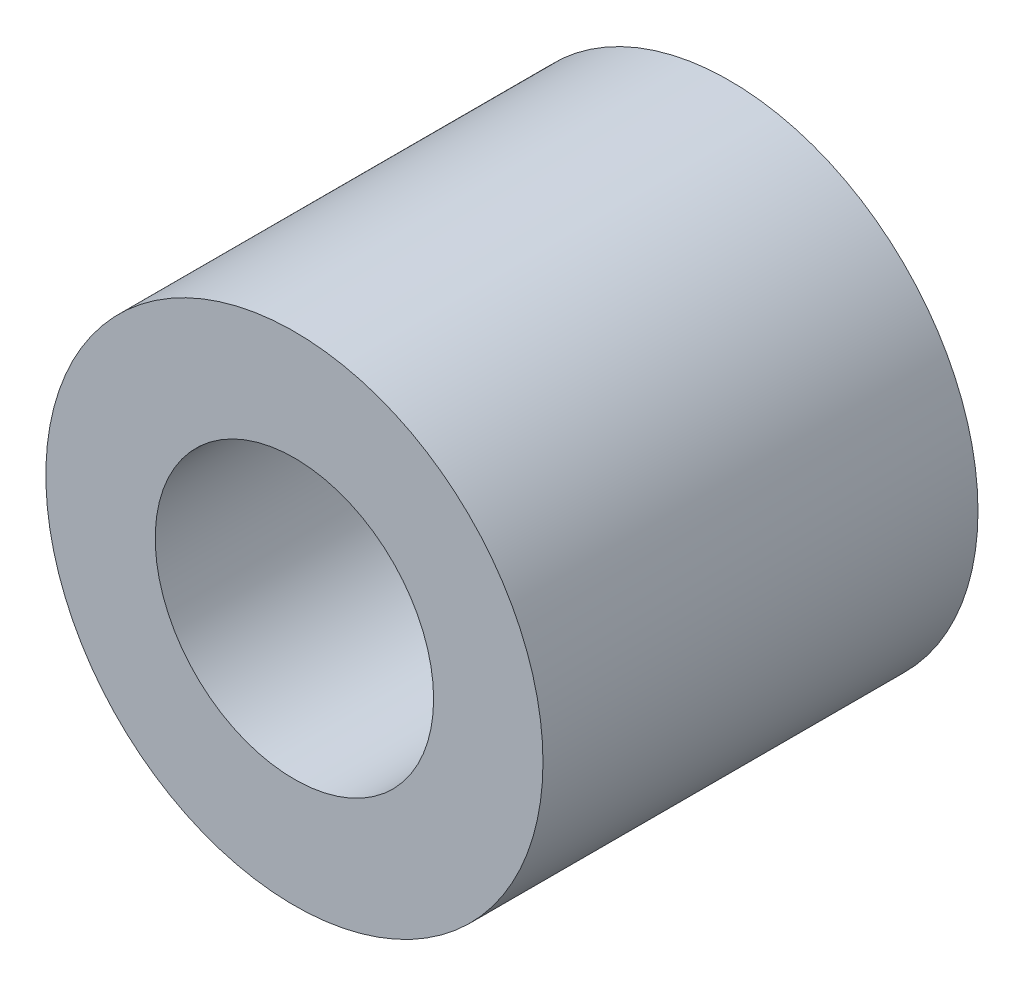
SolidWorks part; units mm, degrees
ref_plane "Front Plane" through (0, 0, 0) normal (0, 0, 1) x (1, 0, 0)
ref_plane "Top Plane" through (0, 0, 0) normal (0, 1, 0) x (1, 0, 0)
ref_plane "Right Plane" through (0, 0, 0) normal (1, 0, 0) x (0, 0, -1)
sketch "Sketch1" plane through (0, 0, 0) normal (0, 0, 1) x (1, 0, 0)
  circle A0 centre (0, 0) radius 3.175
  circle A1 centre (0, 0) radius 1.778
  dimension "OD" = 6.35
  dimension "ID" = 3.556
extrude "Extrude1" add sketch "Sketch1" along normal mid plane 5.5562
sketch "Sketch2" plane through (0, 0, 0) normal (1, 0, 0) x (0, 0, -1)
  line L0 (-2.7781, -1.778) -> (2.7781, -1.778) construction
  line L3 (2.7781, 1.778) -> (-2.7781, 1.778) construction
  line L5 (-2.7781, -1.778) -> (2.7781, -1.778)
  line L6 (2.7781, 1.778) -> (-2.7781, 1.778)
sketch "Sketch4" plane through (0, 0, 2.7781) normal (0, 0, 1) x (1, 0, 0)
  line L0 (0, 0) -> (-1.2572, 1.2572)
  line L1 (0, -3.4925) -> (0, 3.4925) construction
  circle A0 centre (0, 0) radius 1.778 construction
  dimension "D1" = 45
